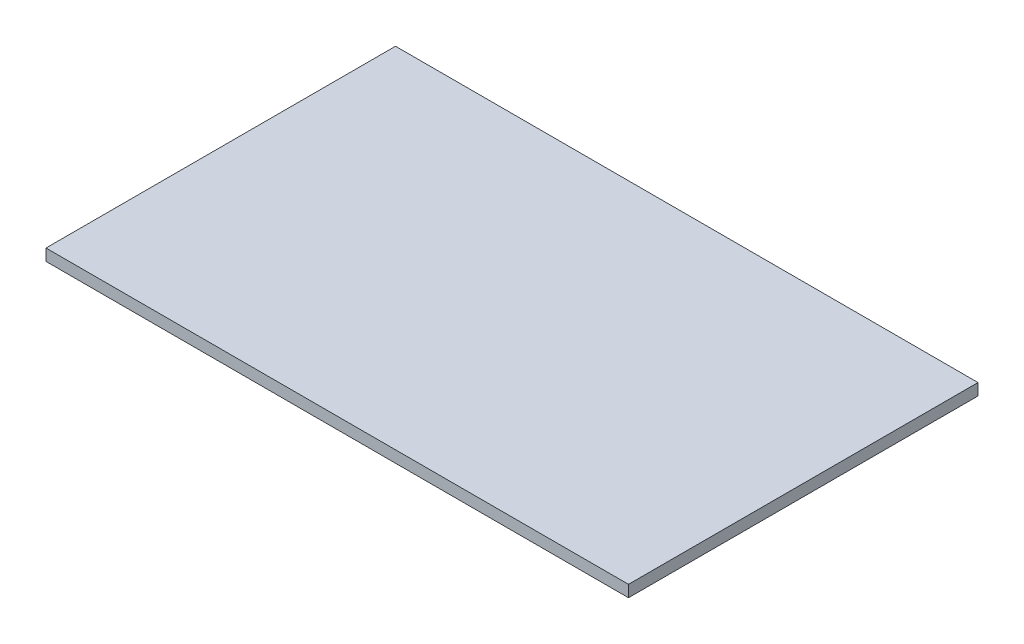
SolidWorks part; units mm, degrees
ref_plane "Front Plane" through (0, 0, 0) normal (0, 0, 1) x (1, 0, 0)
ref_plane "Top Plane" through (0, 0, 0) normal (0, 1, 0) x (1, 0, 0)
ref_plane "Right Plane" through (0, 0, 0) normal (1, 0, 0) x (0, 0, -1)
sketch "Sketch1" plane through (0, 0, 0) normal (0, 1, 0) x (1, 0, 0)
  line L1 (0, 0) -> (300, 0)
  line L2 (0, 0) -> (0, 180)
  line L3 (0, 180) -> (300, 180)
  line L4 (300, 0) -> (300, 180)
  dimension "D1" = 180
  dimension "D2" = 300
extrude "Boss-Extrude1" add sketch "Sketch1" along normal blind 6
